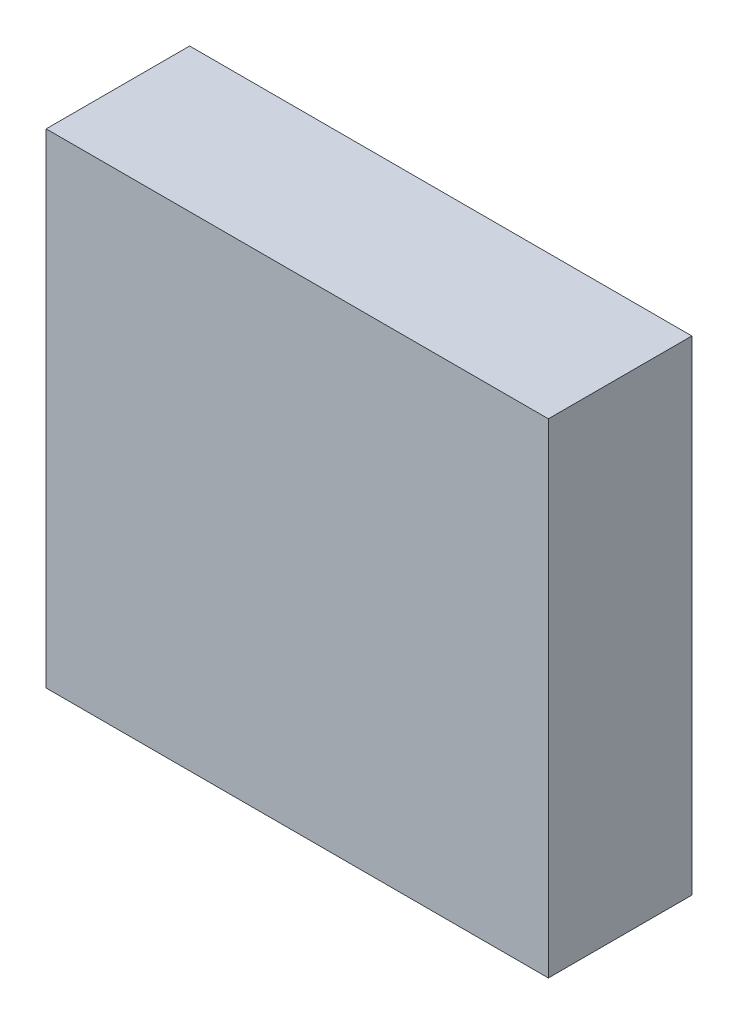
SolidWorks part; units mm, degrees
material "A-玻璃纤维"
ref_plane "前视基准面" through (0, 0, 0) normal (0, 0, 1) x (1, 0, 0)
ref_plane "上视基准面" through (0, 0, 0) normal (0, 1, 0) x (1, 0, 0)
ref_plane "右视基准面" through (0, 0, 0) normal (1, 0, 0) x (0, 0, -1)
sketch "草图1" plane through (0, 0, 0) normal (0, 0, 1) x (1, 0, 0)
  line L1 (0, 0) -> (-28, 0)
  line L2 (0, 0) -> (0, -27)
  line L3 (0, -27) -> (-28, -27)
  line L4 (-28, 0) -> (-28, -27)
  dimension "D1" = 28
  dimension "D2" = 27
extrude "凸台-拉伸1" add sketch "草图1" along normal blind 8
